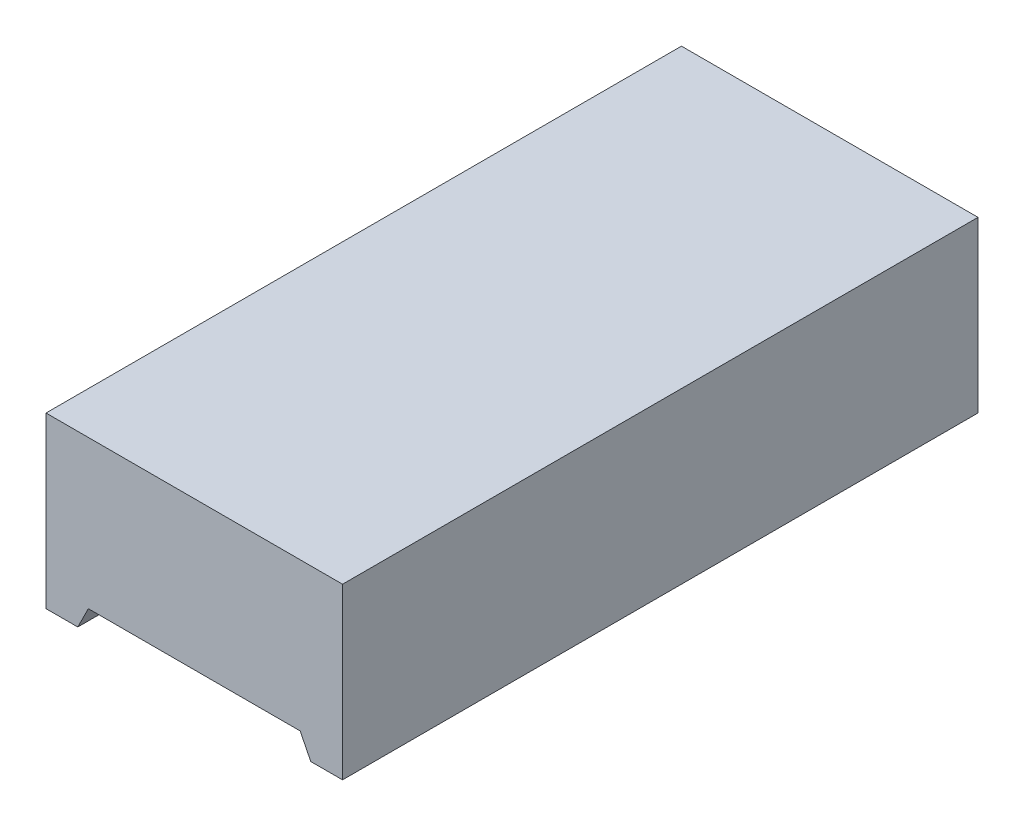
SolidWorks part; units mm, degrees
ref_plane "Plan de face" through (0, 0, 0) normal (0, 0, 1) x (1, 0, 0)
ref_plane "Plan de dessus" through (0, 0, 0) normal (0, 1, 0) x (1, 0, 0)
ref_plane "Plan de droite" through (0, 0, 0) normal (1, 0, 0) x (0, 0, -1)
sketch "Esquisse1" plane through (0, 0, 0) normal (0, 0, 1) x (1, 0, 0)
  line L0 (0, 8.3211) -> (0, 0) construction
  line L1 (7, 0) -> (7, 8)
  line L2 (7, 8) -> (-7, 8)
  line L3 (7, 0) -> (5.5, 0)
  line L4 (5.5, 0) -> (5, 1)
  line L5 (5, 1) -> (-5, 1)
  line L6 (-5.5, 0) -> (-5, 1)
  line L7 (-7, 0) -> (-5.5, 0)
  line L8 (-7, 0) -> (-7, 8)
  point P10 (0, 1)
  point P13 (0, 8)
  dimension "D1" = 7
  dimension "D2" = 8
  dimension "D3" = 1
  dimension "D4" = 1.5
  dimension "D5" = 5
extrude "Boss.-Extru.1" add sketch "Esquisse1" along normal mid plane 30
